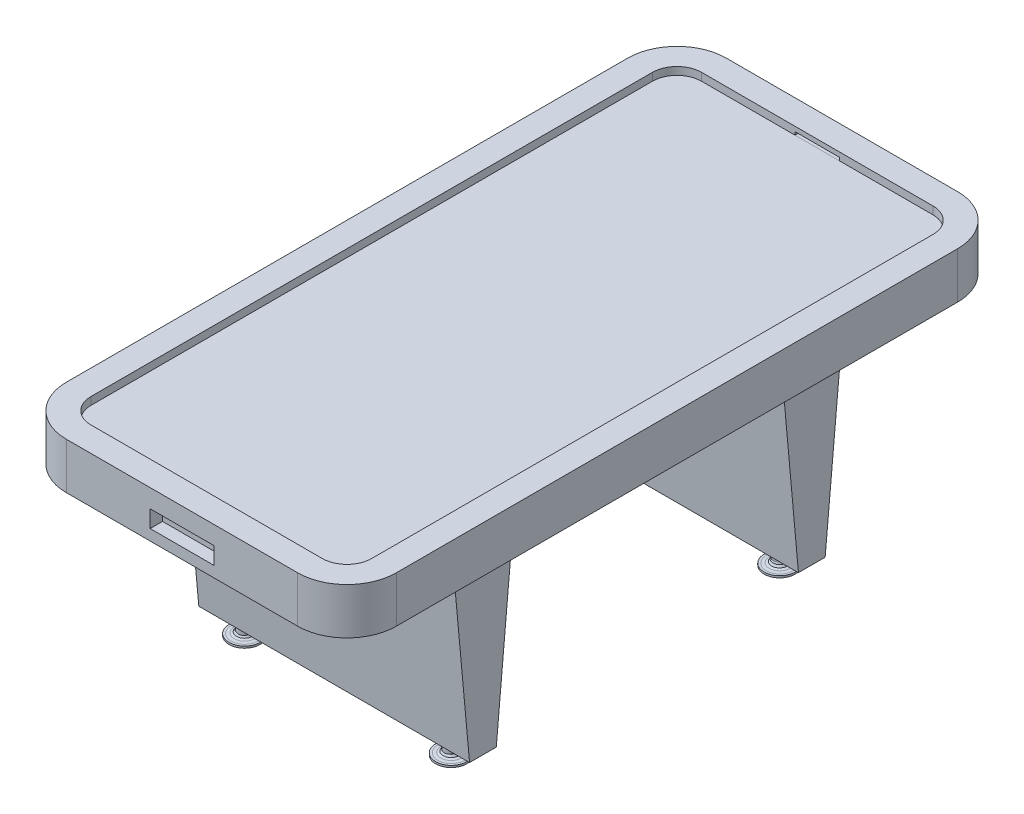
SolidWorks part; units mm, degrees
ref_plane "Front Plane" through (0, 0, 0) normal (0, 0, 1) x (1, 0, 0)
ref_plane "Top Plane" through (0, 0, 0) normal (0, 1, 0) x (1, 0, 0)
ref_plane "Right Plane" through (0, 0, 0) normal (1, 0, 0) x (0, 0, -1)
sketch "Sketch1" plane through (0, 0, 0) normal (0, 1, 0) x (1, 0, 0)
  line L0 (-535, 910) -> (-535, -910)
  line L1 (-375, 990) -> (375, 990)
  line L2 (-455, 910) -> (-455, -910)
  line L3 (-375, -990) -> (375, -990)
  line L4 (455, 910) -> (455, -910)
  line L5 (-455, 990) -> (455, -990) construction
  line L6 (-455, -990) -> (455, 990) construction
  line L7 (-375, -1070) -> (375, -1070)
  line L8 (535, 910) -> (535, -910)
  line L9 (-375, 1070) -> (375, 1070)
  arc A0 (-455, -910) -> (-375, -990) centre (-375, -910) ccw
  arc A1 (375, -990) -> (455, -910) centre (375, -910) ccw
  arc A2 (375, 990) -> (455, 910) centre (375, 910) cw
  arc A3 (-375, 990) -> (-455, 910) centre (-375, 910) ccw
  arc A4 (-535, -910) -> (-375, -1070) centre (-375, -910) ccw
  arc A5 (375, -1070) -> (535, -910) centre (375, -910) ccw
  arc A6 (375, 1070) -> (535, 910) centre (375, 910) cw
  arc A7 (-375, 1070) -> (-535, 910) centre (-375, 910) ccw
  point P0 (0, 0)
  dimension "D3" = 80
  dimension "D1" = 1980
  dimension "D2" = 910
  dimension "D4" = 80
extrude "Boss-Extrude1" add sketch "Sketch1" along normal blind 150
sketch "Sketch3" plane through (0, 0, 0) normal (0, -1, 0) x (1, 0, 0)
  line L1 (-471.6406, -1004.1781) -> (471.6406, -1004.1781)
  line L2 (-471.6406, -1004.1781) -> (-471.6406, 1004.1781)
  line L3 (-471.6406, 1004.1781) -> (471.6406, 1004.1781)
  line L4 (471.6406, -1004.1781) -> (471.6406, 1004.1781)
  line L5 (-471.6406, -1004.1781) -> (471.6406, 1004.1781) construction
  line L6 (-471.6406, 1004.1781) -> (471.6406, -1004.1781) construction
  point P0 (0, 0)
extrude "Boss-Extrude2" add sketch "Sketch3" against normal offset from surface (125 mm away) 25 up to face at (0, 150, 0)
sketch "Sketch4" plane through (0, 0, 0) normal (0, -1, 0) x (1, 0, 0)
  line L0 (0, 0) -> (760.5903, 0) construction
  line L1 (438.876, 631.4244) -> (-438.876, 631.4244)
  line L2 (438.876, 631.4244) -> (438.876, 435.5148)
  line L3 (438.876, 435.5148) -> (-438.876, 435.5148)
  line L4 (-438.876, 631.4244) -> (-438.876, 435.5148)
  line L5 (438.876, 631.4244) -> (-438.876, 435.5148) construction
  line L6 (438.876, 435.5148) -> (-438.876, 631.4244) construction
  line L7 (438.876, -435.5148) -> (-438.876, -435.5148)
  line L8 (-438.876, -631.4244) -> (-438.876, -435.5148)
  line L9 (438.876, -631.4244) -> (-438.876, -631.4244)
  line L10 (438.876, -631.4244) -> (438.876, -435.5148)
  point P0 (0, 533.4696)
extrude "Boss-Extrude3" add sketch "Sketch4" along normal blind 670
sketch "Sketch5" plane through (438.876, 0, 0) normal (1, 0, 0) x (0, 0, -1)
  line L0 (-576.4921, -597.7153) -> (-631.4244, 0)
  line L2 (-631.4244, 0) -> (-813.9914, -798.6823)
  line L3 (-813.9914, -798.6823) -> (-322.4248, -798.6823)
  line L4 (-322.4248, -798.6823) -> (-435.5148, 0)
  line L5 (-435.5148, 0) -> (-489.7809, -597.7153)
  line L6 (-496.3436, -670) -> (-569.8488, -670) construction
  line L7 (0, 0) -> (0, -86.5999) construction
  line L8 (-910, 0) -> (910, 0) construction
  line L9 (435.5148, 0) -> (489.7809, -597.7153)
  line L10 (322.4248, -798.6823) -> (435.5148, 0)
  line L11 (813.9914, -798.6823) -> (322.4248, -798.6823)
  line L12 (631.4244, 0) -> (813.9914, -798.6823)
  line L13 (576.4921, -597.7153) -> (631.4244, 0)
  line L14 (-576.4921, -597.7153) -> (-489.7809, -597.7153)
  line L15 (489.7809, -597.7153) -> (576.4921, -597.7153)
extrude "Cut-Extrude1" cut sketch "Sketch5" against normal blind 1095
sketch "Sketch6" plane through (0, -597.7153, 0) normal (0, -1, 0) x (1, 0, 0)
  line L0 (438.876, -533.4696) -> (-49561.124, -533.4696) construction
  line L1 (438.876, -631.4244) -> (438.876, -435.5148) construction
  line L2 (0, 0) -> (0, 50000) construction
  line L3 (0, 0) -> (-50000, 0) construction
  circle A0 centre (334.3588, -533.4696) radius 20.3776
  circle A1 centre (-334.3588, -533.4696) radius 20.3776
  circle A2 centre (-334.3588, 533.4696) radius 20.3776
  circle A3 centre (334.3588, 533.4696) radius 20.3776
  point P4 (438.876, -533.4696)
extrude "Boss-Extrude4" add sketch "Sketch6" along normal blind 40
sketch "Sketch7" plane through (0, -637.7153, 0) normal (0, -1, 0) x (1, 0, 0)
  line L1 (375.114, -553.8472) -> (334.3588, -553.8472)
  line L2 (375.114, -553.8472) -> (375.114, -513.092)
  line L3 (375.114, -513.092) -> (334.3588, -513.092)
  line L4 (334.3588, -553.8472) -> (334.3588, -513.092)
  line L5 (375.114, -553.8472) -> (334.3588, -513.092) construction
  line L6 (375.114, -513.092) -> (334.3588, -553.8472) construction
  circle A0 centre (334.3588, -533.4696) radius 20.3776 construction
  circle A1 centre (334.3588, -533.4696) radius 20.3776 construction
  point P0 (354.7364, -533.4696)
extrude "Cut-Extrude2" cut sketch "Sketch7" against normal blind 10
sketch "Sketch8" plane through (334.3588, 0, 0) normal (1, 0, 0) x (0, 0, -1)
  line L0 (513.092, -627.7153) -> (511.5264, -633.6801)
  line L1 (511.5264, -633.6801) -> (507.4204, -640.0445)
  line L2 (507.4204, -640.0445) -> (500.2348, -643.2267)
  line L3 (500.2348, -643.2267) -> (490.175, -644.8691)
  line L4 (490.175, -644.8691) -> (483.1948, -644.8691)
  line L5 (483.1948, -644.8691) -> (483.1948, -651.0281)
  line L6 (483.1948, -651.0281) -> (533.4696, -651.0281)
  line L7 (533.4696, -651.0281) -> (533.4696, -627.7153)
  line L8 (513.092, -627.7153) -> (553.8472, -627.7153) construction
  line L9 (533.4696, -627.7153) -> (513.092, -627.7153)
revolve "Revolve1" add sketch "Sketch8" angle 360 about L7
pattern_linear "LPattern1" count 2 spacing 670 along (-1, 0, 0) count 2 spacing 1065 along (0, 0, 1) of "Revolve1"
sketch "Sketch9" plane through (0, 0, 1070) normal (0, 0, 1) x (1, 0, 0)
  line L1 (-103.045, 90.6397) -> (103.045, 90.6397)
  line L2 (-103.045, 90.6397) -> (-103.045, 35.1037)
  line L3 (-103.045, 35.1037) -> (103.045, 35.1037)
  line L4 (103.045, 90.6397) -> (103.045, 35.1037)
  line L5 (-103.045, 90.6397) -> (103.045, 35.1037) construction
  line L6 (-103.045, 35.1037) -> (103.045, 90.6397) construction
  point P0 (0, 62.8717)
extrude "Cut-Extrude3" cut sketch "Sketch9" against normal blind 40
sketch "Sketch10" plane through (0, 0, 990) normal (0, 0, -1) x (-1, 0, 0)
  line L1 (-72.5553, 134.8865) -> (72.5553, 134.8865)
  line L2 (-72.5553, 134.8865) -> (-72.5553, 124.8865)
  line L3 (-72.5553, 124.8865) -> (72.5553, 124.8865)
  line L4 (72.5553, 134.8865) -> (72.5553, 124.8865)
  line L5 (-72.5553, 134.8865) -> (72.5553, 124.8865) construction
  line L6 (-72.5553, 124.8865) -> (72.5553, 134.8865) construction
  point P0 (0, 129.8865)
  dimension "D1" = 10
extrude "Cut-Extrude4" cut sketch "Sketch10" against normal blind 40
mirror "Mirror1" about plane through (0, 0, 0) normal (0, 0, 1) of "Cut-Extrude4", "Cut-Extrude3"
